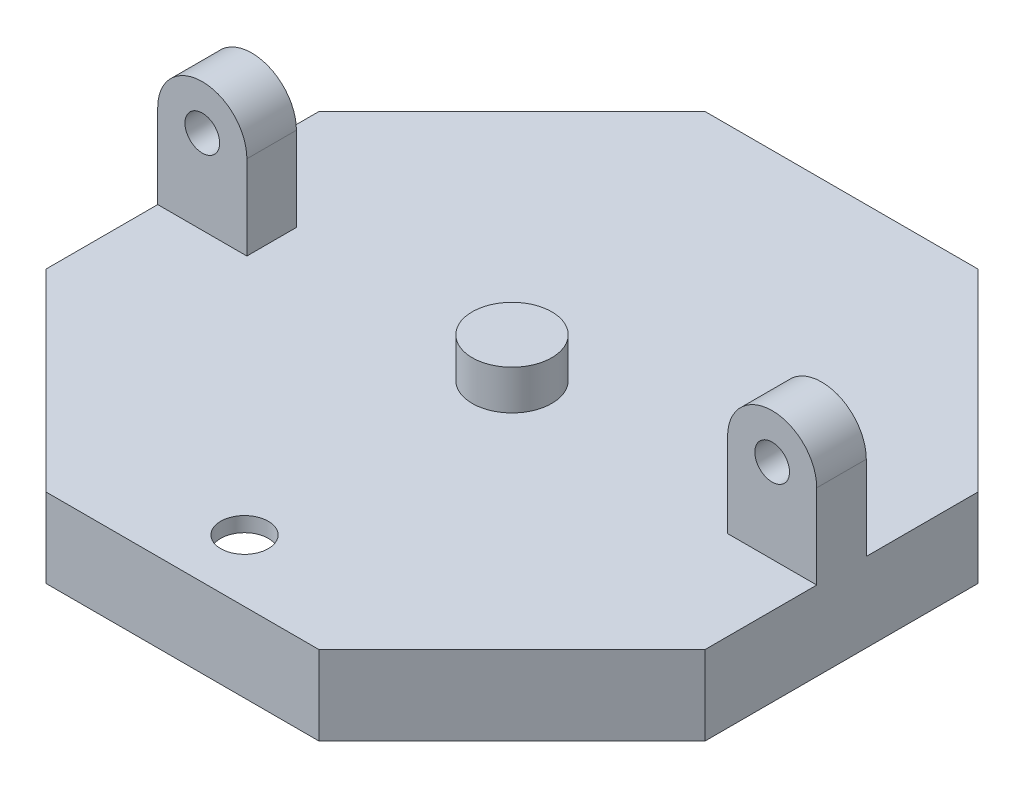
SolidWorks part; units mm, degrees
ref_plane "정면" through (0, 0, 0) normal (0, 0, 1) x (1, 0, 0)
ref_plane "윗면" through (0, 0, 0) normal (0, 1, 0) x (1, 0, 0)
ref_plane "우측면" through (0, 0, 0) normal (1, 0, 0) x (0, 0, -1)
sketch "스케치1" plane through (0, 0, 0) normal (0, 1, 0) x (1, 0, 0)
  line L0 (-55, 0) -> (55, 0) construction
  line L1 (-32.0597, 13.2795) -> (-32.0597, -13.2795)
  line L2 (-32.0597, -13.2795) -> (-13.2795, -32.0597)
  line L3 (-13.2795, -32.0597) -> (13.2795, -32.0597)
  line L4 (13.2795, -32.0597) -> (32.0597, -13.2795)
  line L5 (32.0597, -13.2795) -> (32.0597, 13.2795)
  line L6 (32.0597, 13.2795) -> (13.2795, 32.0597)
  line L7 (13.2795, 32.0597) -> (-13.2795, 32.0597)
  line L8 (-13.2795, 32.0597) -> (-32.0597, 13.2795)
  line L9 (-33.2597, 13.7766) -> (-33.2597, -13.7766)
  line L10 (-33.2597, -13.7766) -> (-13.7766, -33.2597)
  line L11 (-13.7766, -33.2597) -> (13.7766, -33.2597)
  line L12 (13.7766, -33.2597) -> (33.2597, -13.7766)
  line L13 (33.2597, -13.7766) -> (33.2597, 13.7766)
  line L14 (33.2597, 13.7766) -> (13.7766, 33.2597)
  line L15 (13.7766, 33.2597) -> (-13.7766, 33.2597)
  line L16 (-13.7766, 33.2597) -> (-33.2597, 13.7766)
  circle A0 centre (0, 0) radius 34.7011 construction
  dimension "D1" = 72
  dimension "D2" = 1.2
extrude "보스-돌출1" add sketch "스케치1" along normal blind 1.5 contours L7 L8 L1 L2 L3 L4 L5 L6 | L15 L16 L9 L10 L11 L12 L13 L14 L8 L7 L6 L5 L4 L3 L2 L1
sketch "스케치2" plane through (0, 0, 0) normal (0, -1, 0) x (1, 0, 0)
  line L8 (-12.7825, -30.8597) -> (12.7825, -30.8597)
  line L9 (12.7825, -30.8597) -> (30.8597, -12.7825)
  line L10 (30.8597, -12.7825) -> (30.8597, 12.7825)
  line L11 (30.8597, 12.7825) -> (12.7825, 30.8597)
  line L12 (12.7825, 30.8597) -> (-12.7825, 30.8597)
  line L13 (-12.7825, 30.8597) -> (-30.8597, 12.7825)
  line L14 (-30.8597, 12.7825) -> (-30.8597, -12.7825)
  line L15 (-30.8597, -12.7825) -> (-12.7825, -30.8597)
  line L16 (-13.2795, -32.0597) -> (13.2795, -32.0597)
  line L17 (13.2795, -32.0597) -> (32.0597, -13.2795)
  line L18 (32.0597, -13.2795) -> (32.0597, 13.2795)
  line L19 (32.0597, 13.2795) -> (13.2795, 32.0597)
  line L20 (13.2795, 32.0597) -> (-13.2795, 32.0597)
  line L21 (-13.2795, 32.0597) -> (-32.0597, 13.2795)
  line L22 (-32.0597, 13.2795) -> (-32.0597, -13.2795)
  line L23 (-32.0597, -13.2795) -> (-13.2795, -32.0597)
  line L24 (-13.2795, -32.0597) -> (13.2795, -32.0597)
  line L25 (13.2795, -32.0597) -> (32.0597, -13.2795)
  line L26 (32.0597, -13.2795) -> (32.0597, 13.2795)
  line L27 (32.0597, 13.2795) -> (13.2795, 32.0597)
  line L28 (13.2795, 32.0597) -> (-13.2795, 32.0597)
  line L29 (-13.2795, 32.0597) -> (-32.0597, 13.2795)
  line L30 (-32.0597, 13.2795) -> (-32.0597, -13.2795)
  line L31 (-32.0597, -13.2795) -> (-13.2795, -32.0597)
  line L32 (-12.2854, -29.6597) -> (12.2854, -29.6597)
  line L33 (12.2854, -29.6597) -> (29.6597, -12.2854)
  line L34 (29.6597, -12.2854) -> (29.6597, 12.2854)
  line L35 (29.6597, 12.2854) -> (12.2854, 29.6597)
  line L36 (12.2854, 29.6597) -> (-12.2854, 29.6597)
  line L37 (-12.2854, 29.6597) -> (-29.6597, 12.2854)
  line L38 (-29.6597, 12.2854) -> (-29.6597, -12.2854)
  line L39 (-29.6597, -12.2854) -> (-12.2854, -29.6597)
  line M17 (-13.7766, -33.2597) -> (13.7766, -33.2597)
  line M18 (13.7766, -33.2597) -> (33.2597, -13.7766)
  line M19 (33.2597, -13.7766) -> (33.2597, 13.7766)
  line M20 (33.2597, 13.7766) -> (13.7766, 33.2597)
  line M21 (13.7766, 33.2597) -> (-13.7766, 33.2597)
  line M22 (-13.7766, 33.2597) -> (-33.2597, 13.7766)
  line M23 (-33.2597, 13.7766) -> (-33.2597, -13.7766)
  line M24 (-33.2597, -13.7766) -> (-13.7766, -33.2597)
  dimension "D1" = 1.2
  dimension "D2" = 1.2
  dimension "D3" = 1.2
extrude "보스-돌출2" add sketch "스케치2" along normal blind 6.5 contours L31 L30 L29 L28 L27 L26 L25 L24 M24 M17 M18 M19 M20 M21 M22 M23 | L30 L31 L24 L25 L26 L27 L28 L29 L15 L14 L13 L12 L11 L10 L9 L8 | L14 L15 L8 L9 L10 L11 L12 L13 L39 L38 L37 L36 L35 L34 L33 L32
sketch "스케치3" plane through (0, -6.5, 0) normal (0, -1, 0) x (1, 0, 0)
  line L8 (-30.8597, -12.7825) -> (-12.7825, -30.8597)
  line L9 (-12.7825, -30.8597) -> (12.7825, -30.8597)
  line L10 (12.7825, -30.8597) -> (30.8597, -12.7825)
  line L11 (30.8597, -12.7825) -> (30.8597, 12.7825)
  line L12 (30.8597, 12.7825) -> (12.7825, 30.8597)
  line L13 (12.7825, 30.8597) -> (-12.7825, 30.8597)
  line L14 (-12.7825, 30.8597) -> (-30.8597, 12.7825)
  line L15 (-30.8597, 12.7825) -> (-30.8597, -12.7825)
  line L16 (-32.0597, -13.2795) -> (-13.2795, -32.0597)
  line L17 (-13.2795, -32.0597) -> (13.2795, -32.0597)
  line L18 (13.2795, -32.0597) -> (32.0597, -13.2795)
  line L19 (32.0597, -13.2795) -> (32.0597, 13.2795)
  line L20 (32.0597, 13.2795) -> (13.2795, 32.0597)
  line L21 (13.2795, 32.0597) -> (-13.2795, 32.0597)
  line L22 (-13.2795, 32.0597) -> (-32.0597, 13.2795)
  line L23 (-32.0597, 13.2795) -> (-32.0597, -13.2795)
  line L24 (-32.0597, -13.2795) -> (-13.2795, -32.0597)
  line L25 (-13.2795, -32.0597) -> (13.2795, -32.0597)
  line L26 (13.2795, -32.0597) -> (32.0597, -13.2795)
  line L27 (32.0597, -13.2795) -> (32.0597, 13.2795)
  line L28 (32.0597, 13.2795) -> (13.2795, 32.0597)
  line L29 (13.2795, 32.0597) -> (-13.2795, 32.0597)
  line L30 (-13.2795, 32.0597) -> (-32.0597, 13.2795)
  line L31 (-32.0597, 13.2795) -> (-32.0597, -13.2795)
  dimension "D1" = 1.2
  dimension "D2" = 1.2
extrude "컷-돌출1" cut sketch "스케치3" against normal blind 1
sketch "스케치4" plane through (0, 1.5, 0) normal (0, 1, 0) x (1, 0, 0)
  circle A0 centre (0, 0) radius 4.015
  dimension "D1" = 8.03
extrude "보스-돌출3" add sketch "스케치4" along normal blind 4
sketch "스케치6" plane through (0, 0, 0) normal (0, -1, 0) x (1, 0, 0)
  circle A3 centre (0, 0) radius 4.015
  circle A4 centre (0, 0) radius 4.015
  dimension "D1" = 0
extrude "보스-돌출4" add sketch "스케치6" along normal blind 4
sketch "스케치7" plane through (0, 1.5, 0) normal (0, 1, 0) x (1, 0, 0)
  line L1 (0, -4.4) -> (0, 4.4) construction
  circle A0 centre (0, -27) radius 2.4
  dimension "D1" = 4.8
  dimension "D2" = 27
extrude "컷-돌출3" cut sketch "스케치7" against normal through all
sketch "스케치8" plane through (0, 1.5, 0) normal (0, 1, 0) x (1, 0, 0)
  line L0 (-33.2597, 13.7766) -> (-33.2597, -13.7766) construction
  line L1 (-33.2597, 2.5) -> (-24.2597, 2.5)
  line L2 (-33.2597, 2.5) -> (-33.2597, -2.5)
  line L3 (-33.2597, -2.5) -> (-24.2597, -2.5)
  line L4 (-24.2597, 2.5) -> (-24.2597, -2.5)
  dimension "D2" = 9
  dimension "D3" = 5
  dimension "D4" = 2.5
extrude "보스-돌출5" add sketch "스케치8" along normal blind 8.5
sketch "스케치9" plane through (0, 10, 0) normal (0, 1, 0) x (1, 0, 0)
  line L0 (-28.7597, 5.5088) -> (-28.7597, -6.7586) construction
  line L1 (-33.2597, 2.5) -> (-33.2597, -2.5) construction
  line L6 (-33.2597, 2.5) -> (-33.2597, -2.5)
  line L7 (-33.2597, -2.5) -> (-24.2597, -2.5)
  line L8 (-24.2597, -2.5) -> (-24.2597, 2.5)
  line L9 (-24.2597, 2.5) -> (-33.2597, 2.5)
  line L10 (-33.2597, 2.5) -> (-33.2597, -2.5)
  line L11 (-33.2597, -2.5) -> (-24.2597, -2.5)
  line L12 (-24.2597, -2.5) -> (-24.2597, 2.5)
  line L13 (-24.2597, 2.5) -> (-33.2597, 2.5)
  dimension "D1" = 4.5
  dimension "D2" = 0
revolve "회전1" add sketch "스케치9" angle 360 about L0
sketch "스케치10" plane through (0, 0, 2.5) normal (0, 0, 1) x (1, 0, 0)
  circle A0 centre (-28.7597, 10) radius 1.75
  arc A4 (-24.2597, 10) -> (-33.2597, 10) centre (-28.7597, 10) ccw construction
  dimension "D1" = 3.5
extrude "컷-돌출4" cut sketch "스케치10" against normal through all
mirror "대칭 복사1" about plane through (0, 0, 0) normal (1, 0, 0) of "컷-돌출4", "회전1", "보스-돌출5"
